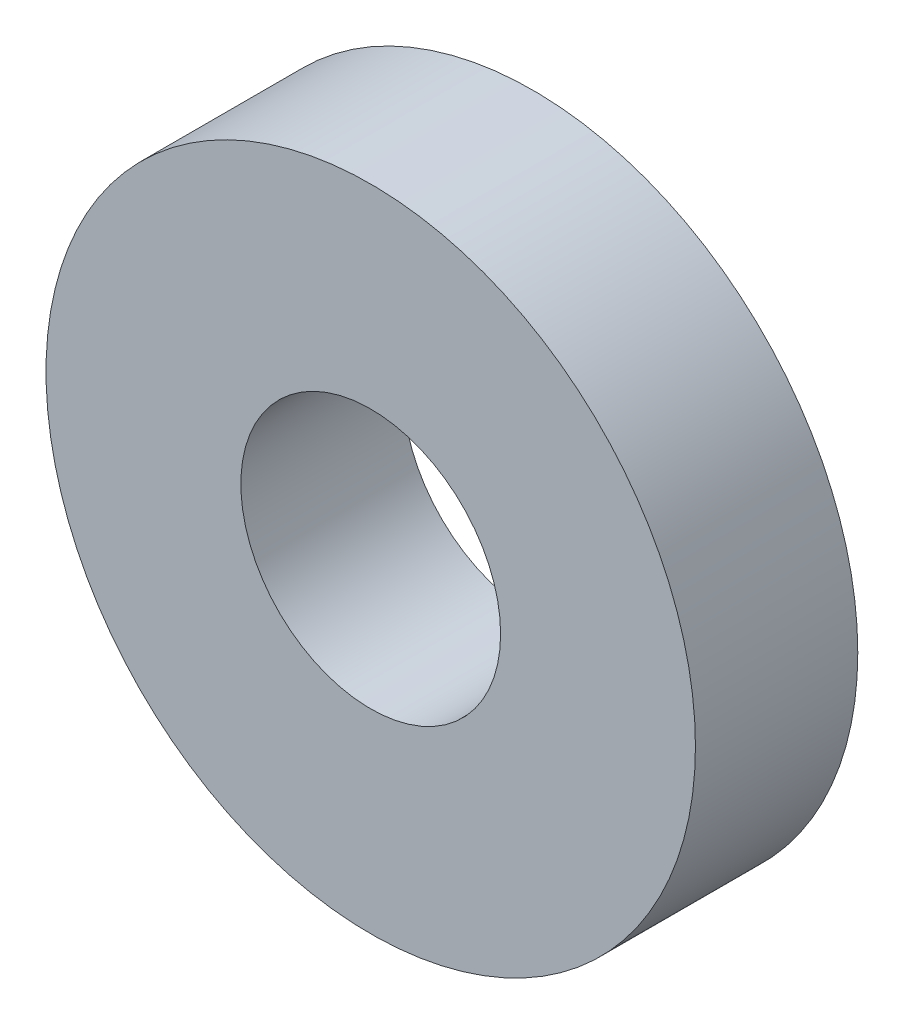
SolidWorks part; units mm, degrees
ref_plane "Front Plane" through (0, 0, 0) normal (0, 0, 1) x (1, 0, 0)
ref_plane "Top Plane" through (0, 0, 0) normal (0, 1, 0) x (1, 0, 0)
ref_plane "Right Plane" through (0, 0, 0) normal (1, 0, 0) x (0, 0, -1)
sketch "Sketch1" plane through (0, 0, 0) normal (0, 0, 1) x (1, 0, 0)
  circle A0 centre (0, 0) radius 2
  circle A1 centre (0, 0) radius 5
  dimension "D1" = 4
  dimension "D2" = 3
extrude "Boss-Extrude1" add sketch "Sketch1" along normal blind 2.5
